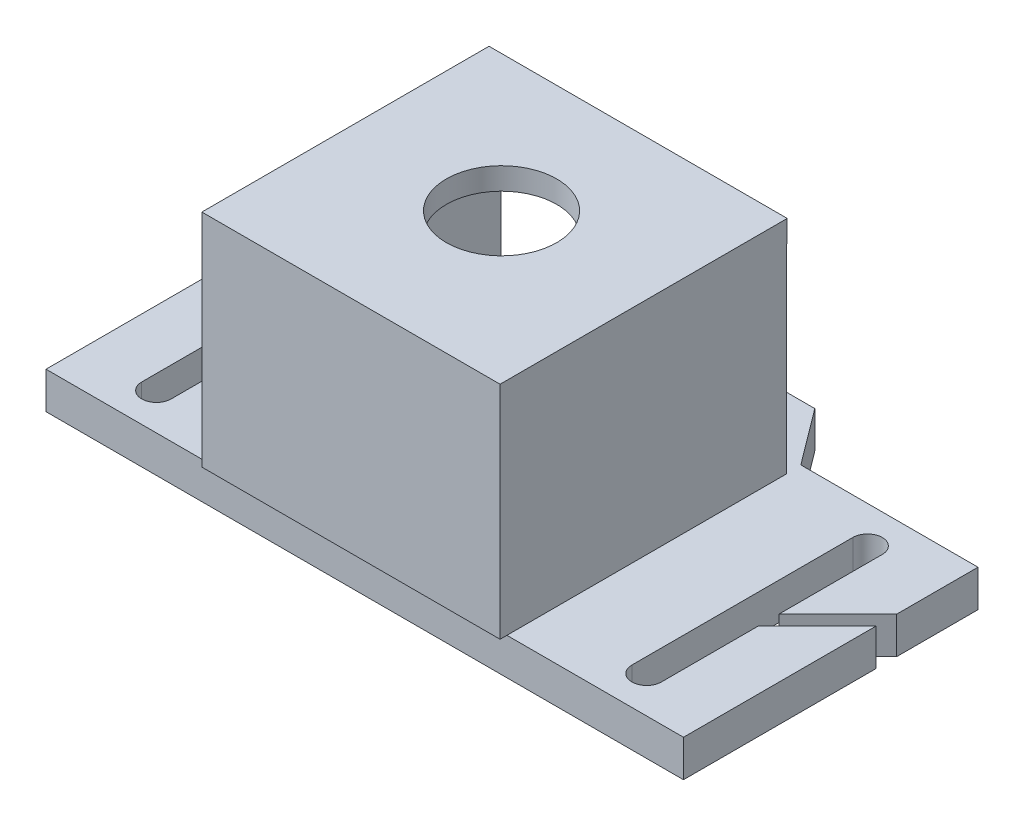
SolidWorks part; units mm, degrees
ref_plane "前视基准面" through (0, 0, 0) normal (0, 0, 1) x (1, 0, 0)
ref_plane "上视基准面" through (0, 0, 0) normal (0, 1, 0) x (1, 0, 0)
ref_plane "右视基准面" through (0, 0, 0) normal (1, 0, 0) x (0, 0, -1)
sketch "草图1" plane through (0, 0, 0) normal (0, 1, 0) x (1, 0, 0)
  line L0 (13.5457, 26.4282) -> (-13.5457, 26.4282)
  line L1 (-13.5457, 26.4282) -> (-19.2291, 18.8502)
  line L2 (-19.2291, 18.8502) -> (-43.2893, 18.8502)
  line L3 (-43.2893, 18.8502) -> (-43.2893, -21.1498)
  line L4 (-43.2893, -21.1498) -> (43.2893, -21.1498)
  line L5 (43.2893, 18.8502) -> (43.2893, -21.1498)
  line L6 (19.2291, 18.8502) -> (43.2893, 18.8502)
  line L7 (13.5457, 26.4282) -> (19.2291, 18.8502)
  point P9 (0, 26.4282)
  dimension "D1" = 40
extrude "凸台-拉伸1" add sketch "草图1" along normal blind 5
sketch "草图4" plane through (0, 5, 0) normal (0, 1, 0) x (1, 0, 0)
  line L0 (-43.2893, 18.8502) -> (-43.2893, -21.1498) construction
  line L1 (-21.2893, 16.8502) -> (-19.4893, 16.8502)
  line L2 (-21.2893, 16.8502) -> (-21.2893, -20.1498)
  line L3 (-21.2893, -20.1498) -> (-19.4893, -20.1498)
  line L4 (-19.4893, 16.8502) -> (-19.4893, -20.1498)
  line L5 (17.5107, 16.8502) -> (19.3107, 16.8502)
  line L6 (17.5107, 16.8502) -> (17.5107, -20.1498)
  line L7 (17.5107, -20.1498) -> (19.3107, -20.1498)
  line L8 (19.3107, 16.8502) -> (19.3107, -20.1498)
  line L10 (-19.2291, 18.8502) -> (-43.2893, 18.8502) construction
  dimension "D1" = 1.8
  dimension "D2" = 1.8
  dimension "D3" = 37
  dimension "D4" = 22
  dimension "D5" = 37
  dimension "D6" = 37
  dimension "D7" = 2
extrude "凸台-拉伸2" add sketch "草图4" along normal blind 27
sketch "草图5" plane through (0, 32, 0) normal (0, 1, 0) x (1, 0, 0)
  line L0 (19.3107, -20.1498) -> (19.3107, 16.8502) construction
  line L1 (-21.1893, 16.9197) -> (19.3107, 16.9197)
  line L2 (-21.1893, 16.9197) -> (-21.1893, -20.0803)
  line L3 (-21.1893, -20.0803) -> (19.3107, -20.0803)
  line L4 (19.3107, 16.9197) -> (19.3107, -20.0803)
  dimension "D1" = 40.5
  dimension "D2" = 37
  dimension "D3" = 0
  dimension "D4" = 37
extrude "凸台-拉伸3" add sketch "草图5" along normal blind 3
sketch "草图8" plane through (0, 5, 0) normal (0, 1, 0) x (1, 0, 0)
  line L0 (-33.2893, 13.8502) -> (-33.2893, -16.1498) construction
  line L1 (-31.2893, 13.8502) -> (-31.2893, -16.1498)
  line L2 (-35.2893, 13.8502) -> (-35.2893, -16.1498)
  line L3 (-19.2291, 18.8502) -> (-43.2893, 18.8502) construction
  line L4 (-43.2893, 18.8502) -> (-43.2893, -21.1498) construction
  arc A0 (-31.2893, 13.8502) -> (-35.2893, 13.8502) centre (-33.2893, 13.8502) ccw
  arc A1 (-35.2893, -16.1498) -> (-31.2893, -16.1498) centre (-33.2893, -16.1498) ccw
  point P2 (-33.2893, -1.1498)
  dimension "D1" = 4
  dimension "D2" = 30
  dimension "D3" = 5
  dimension "D4" = 8
extrude "切除-拉伸4" cut sketch "草图8" against normal blind 10
sketch "草图10" plane through (0, 5, 0) normal (0, 1, 0) x (1, 0, 0)
  line L0 (33.2893, 13.8502) -> (33.2893, -16.1498) construction
  line L1 (35.2893, 13.8502) -> (35.2893, -16.1498)
  line L2 (31.2893, 13.8502) -> (31.2893, -16.1498)
  line L3 (43.2893, 18.8502) -> (19.2291, 18.8502) construction
  line L4 (43.2893, -21.1498) -> (43.2893, 18.8502) construction
  arc A0 (35.2893, 13.8502) -> (31.2893, 13.8502) centre (33.2893, 13.8502) ccw
  arc A1 (31.2893, -16.1498) -> (35.2893, -16.1498) centre (33.2893, -16.1498) ccw
  point P2 (33.2893, -1.1498)
  dimension "D1" = 4
  dimension "D2" = 5
  dimension "D3" = 30
  dimension "D4" = 8
extrude "切除-拉伸7" cut sketch "草图10" against normal blind 10
sketch "草图12" plane through (0, 5, 0) normal (0, 1, 0) x (1, 0, 0)
  line L0 (-45.206, 6.1545) -> (-34.2029, -4.0401) construction
  line L4 (44.0989, 7.1918) -> (33.4923, -3.4148) construction
  line L5 (44.806, 6.4847) -> (34.1994, -4.1219)
  line L6 (43.3917, 7.8989) -> (32.7851, -2.7077)
  line L7 (-44.5264, 6.888) -> (-33.5232, -3.3066)
  line L8 (-45.8857, 5.421) -> (-34.8825, -4.7737)
  arc A2 (44.806, 6.4847) -> (43.3917, 7.8989) centre (44.0989, 7.1918) ccw
  arc A3 (32.7851, -2.7077) -> (34.1994, -4.1219) centre (33.4923, -3.4148) ccw
  arc A4 (-44.5264, 6.888) -> (-45.8857, 5.421) centre (-45.206, 6.1545) ccw
  arc A5 (-34.8825, -4.7737) -> (-33.5232, -3.3066) centre (-34.2029, -4.0401) ccw
  point P2 (-39.7044, 1.0572)
  point P9 (38.7956, 1.8885)
  dimension "D1" = 2
  dimension "D2" = 15
  dimension "D3" = 2
  dimension "D4" = 15
extrude "切除-拉伸8" cut sketch "草图12" against normal blind 10
sketch "草图13" plane through (0, 35, 0) normal (0, 1, 0) x (1, 0, 0)
  line L0 (-21.2893, 16.8502) -> (-21.2893, -20.1498) construction
  line L2 (19.3107, 16.9197) -> (-21.1893, 16.9197) construction
  circle A0 centre (-0.9893, -1.5803) radius 7.5
  dimension "D1" = 15
  dimension "D2" = 20.3
  dimension "D3" = 18.5
extrude "切除-拉伸9" cut sketch "草图13" against normal blind 10
sketch "草图14" plane through (0, 0, 20.0803) normal (0, 0, 1) x (1, 0, 0)
  line L1 (-21.1893, 35) -> (19.3107, 35)
  line L2 (-21.1893, 35) -> (-21.1893, 5)
  line L3 (-21.1893, 5) -> (19.3107, 5)
  line L4 (19.3107, 35) -> (19.3107, 5)
extrude "凸台-拉伸4" add sketch "草图14" along normal blind 2
